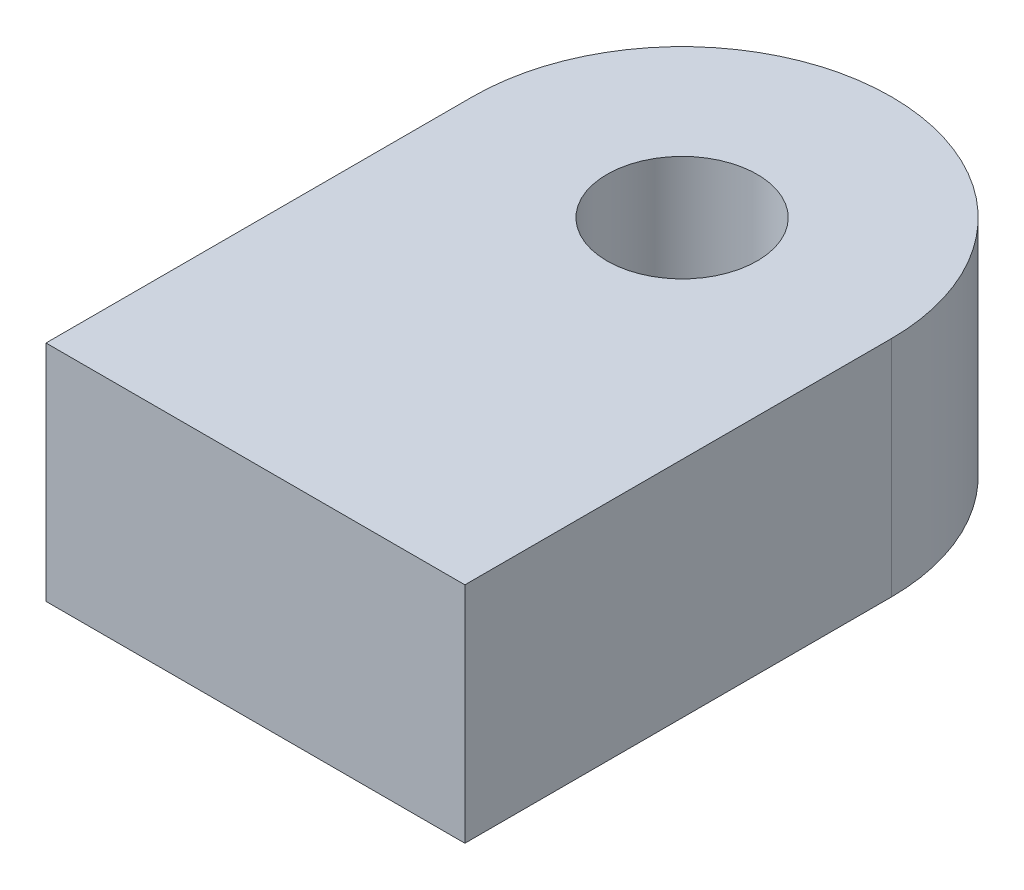
SolidWorks part; units mm, degrees
ref_plane "Front Plane" through (0, 0, 0) normal (0, 0, 1) x (1, 0, 0)
ref_plane "Top Plane" through (0, 0, 0) normal (0, 1, 0) x (1, 0, 0)
ref_plane "Right Plane" through (0, 0, 0) normal (1, 0, 0) x (0, 0, -1)
sketch "Sketch1" plane through (0, 0, 0) normal (0, 1, 0) x (1, 0, 0)
  line L1 (0, 0) -> (31.05, 0)
  line L2 (0, 0) -> (0, 31.62)
  line L3 (15.52, 47.14) -> (15.53, 47.14)
  line L4 (31.05, 0) -> (31.05, 31.62)
  arc A0 (15.53, 47.14) -> (31.05, 31.62) centre (15.53, 31.62) cw
  arc A1 (15.52, 47.14) -> (0, 31.62) centre (15.52, 31.62) ccw
  circle A2 centre (15.53, 31.62) radius 5.565
  point P7 (31.05, 47.14)
  dimension "D3" = 15.52
  dimension "D4" = 11.13
  dimension "D1" = 31.05
  dimension "D2" = 47.14
extrude "Boss-Extrude1" add sketch "Sketch1" along normal blind 16.59
